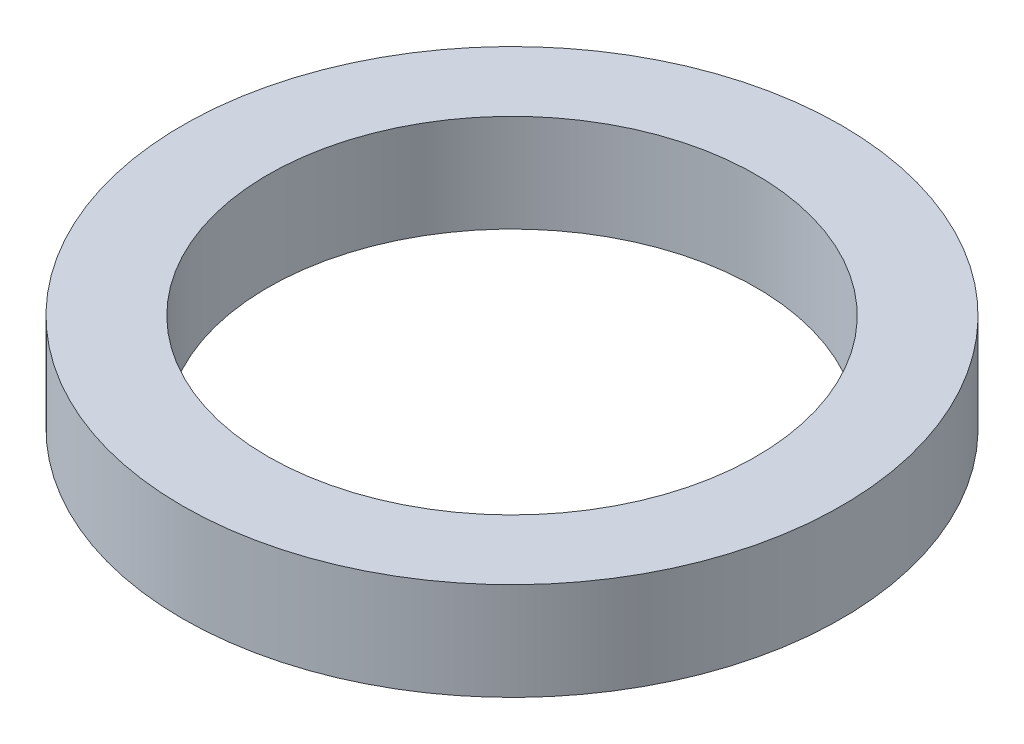
SolidWorks part; units mm, degrees
ref_plane "Front Plane" through (0, 0, 0) normal (0, 0, 1) x (1, 0, 0)
ref_plane "Top Plane" through (0, 0, 0) normal (0, 1, 0) x (1, 0, 0)
ref_plane "Right Plane" through (0, 0, 0) normal (1, 0, 0) x (0, 0, -1)
sketch "Sketch1" plane through (0, 0, 0) normal (0, 1, 0) x (1, 0, 0)
  circle A0 centre (0, 0) radius 10
  circle A1 centre (0, 0) radius 13.5
  dimension "D1" = 20
  dimension "D2" = 27
extrude "Boss-Extrude1" add sketch "Sketch1" along normal blind 4
